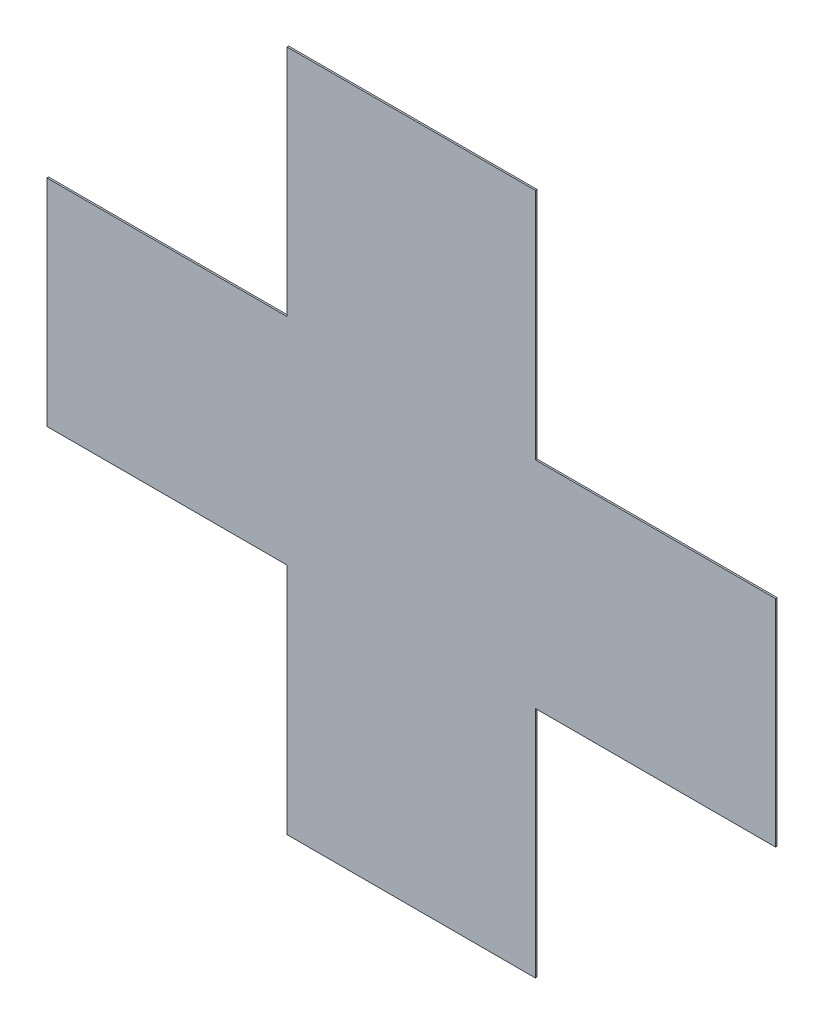
SolidWorks part; units mm, degrees
ref_plane "Front Plane" through (0, 0, 0) normal (0, 0, 1) x (1, 0, 0)
ref_plane "Top Plane" through (0, 0, 0) normal (0, 1, 0) x (1, 0, 0)
ref_plane "Right Plane" through (0, 0, 0) normal (1, 0, 0) x (0, 0, -1)
sketch "Sketch1" plane through (0, 0, 0) normal (0, 0, 1) x (1, 0, 0)
  line L0 (0, -223.5955) -> (0, 432.5843) construction
  line L1 (-345.5056, 0) -> (393.0233, 0) construction
  line L2 (-150, 412) -> (150, 412)
  line L3 (150, 412) -> (150, 130)
  line L4 (150, 130) -> (440, 130)
  line L5 (440, 130) -> (440, -130)
  line L6 (-440, 130) -> (-440, -130)
  line L7 (-150, 130) -> (-440, 130)
  line L8 (-150, 412) -> (-150, 130)
  line L9 (150, -130) -> (440, -130)
  line L10 (150, -412) -> (150, -130)
  line L11 (-150, -412) -> (150, -412)
  line L12 (-150, -412) -> (-150, -130)
  line L13 (-150, -130) -> (-440, -130)
  point P7 (440, 130)
  point P11 (0, 0)
  point P12 (393.0233, 0)
  point P17 (0, 412)
  point P18 (440, 0)
  point P23 (-440, 0)
  dimension "D1" = 150
  dimension "D2" = 290
  dimension "D3" = 282
  dimension "D4" = 130
extrude "Boss-Extrude1" add sketch "Sketch1" along normal blind 2
